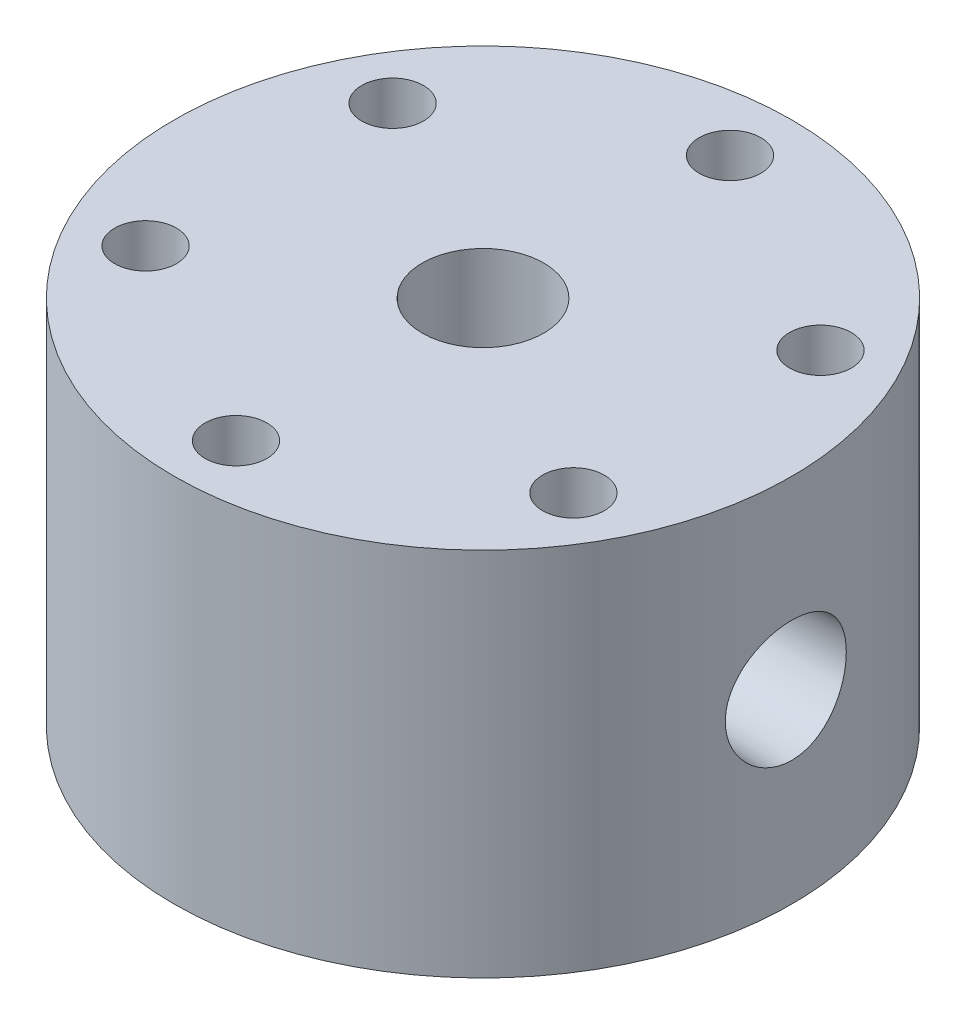
SolidWorks part; units mm, degrees
ref_plane "Front Plane" through (0, 0, 0) normal (0, 0, 1) x (1, 0, 0)
ref_plane "Top Plane" through (0, 0, 0) normal (0, 1, 0) x (1, 0, 0)
ref_plane "Right Plane" through (0, 0, 0) normal (1, 0, 0) x (0, 0, -1)
sketch "Sketch1" plane through (0, 0, 0) normal (0, 0, 1) x (1, 0, 0)
  line L2 (-3.81, 0) -> (-8.0645, 0)
  line L3 (-31.75, -6.35) -> (-31.75, 31.75)
  line L4 (-31.75, 31.75) -> (-3.81, 31.75)
  line L6 (-3.81, 31.75) -> (-3.81, 0)
  line L10 (0, 0) -> (0, 15.7692) construction
  line L11 (-31.75, -6.35) -> (-12.7, -6.35)
  line L12 (-11.1125, 0) -> (-11.1125, 2.032)
  line L13 (-11.1125, 2.032) -> (-8.0645, 2.032)
  line L14 (-8.0645, 2.032) -> (-8.0645, 0)
  line L15 (-11.1125, 0) -> (-12.7, 0)
  line L16 (-12.7, 0) -> (-12.7, -6.35)
  point P1 (0, 0)
  dimension "D1" = 3.81
  dimension "D2" = 1.5875
  dimension "D3" = 12.7
  dimension "D4" = 38.1
  dimension "D5" = 31.75
  dimension "D6" = 6.35
  dimension "D8" = 3.048
  dimension "D9" = 2.032
revolve "Revolve1" add sketch "Sketch1" angle 360 about L10
hole_wizard "M14x1.5 Tapped Hole1" positions "Sketch2" profile "Sketch4" tap size "M14x1.5" standard "ANSI Metric"
sketch "Sketch2" plane through (0, 31.75, 0) normal (0, 1, 0) x (1, 0, 0)
  point P0 (0, 0)
sketch "Sketch4" plane through (0, 31.75, 0) normal (1, 0, 0) x (0, 0, 1)
  line L0 (0, 0) -> (0, 29.1554)
  line L1 (0, 29.1554) -> (6.25, 25.4)
  line L2 (6.25, 25.4) -> (6.25, 0)
  line L5 (6.25, 0) -> (0, 0)
  line L10 (0, 29.1554) -> (-6.25, 25.4) construction
  line L11 (0, -6.35) -> (0, 107.95) construction
  dimension "Tap Drill Dia." = 12.5
  dimension "Tap Drill Depth" = 25.4
  dimension "Drill Angle" = 118
cosmetic thread "Hole Thread3" parameters "D1"=27.94, "D2"=14
ref_plane "Plane1" through (31.75, 0, 0) normal (1, 0, 0) x (0, 0, -1)
ref_plane "Plane2" through (-31.75, 0, 0) normal (-1, 0, 0) x (0, 0, 1)
hole_wizard "1/4 NPT Tapped Hole1" positions "Sketch5" profile "Sketch6" size "1/4" standard "ANSI Inch"
sketch "Sketch5" plane through (31.75, 0, 0) normal (1, 0, 0) x (0, 0, -1)
  line L0 (31.75, 31.75) -> (-31.75, 31.75) construction
  point P0 (0, 12.7)
  dimension "D1" = 19.05
sketch "Sketch6" plane through (31.75, 12.7, 0) normal (0, 1, 0) x (0, 0, -1)
  line L0 (0, 0) -> (0, 20.3603)
  line L1 (5.5626, 17.018) -> (0, 20.3603)
  line L2 (-5.5626, 17.018) -> (0, 20.3603) construction
  line L3 (5.5626, 17.018) -> (5.5626, 9.906)
  line L4 (5.5626, 9.906) -> (5.9437, 9.906)
  line L5 (5.9437, 9.906) -> (6.2403, 0)
  line L6 (-5.9437, 9.906) -> (-6.2403, 0) construction
  line L7 (6.2403, 0) -> (0, 0)
  line L8 (0, -6.35) -> (0, 107.95) construction
  line L11 (-5.5626, 9.906) -> (-5.9437, 9.906) construction
  dimension "Tap Drill Dia." = 11.1252
  dimension "Tap Drill Depth" = 17.018
  dimension "Thread Dia." = 12.4806
  dimension "Thread Angle" = 3.43
  dimension "Thread Depth" = 9.906
  dimension "Drill Angle" = 118
cosmetic thread "Hole Thread1" parameters "D1"=9.906, "D2"=13.7086
hole_wizard "1/4 NPT Tapped Hole2" positions "Sketch7" profile "Sketch8" size "1/4" standard "ANSI Inch"
sketch "Sketch7" plane through (-31.75, 0, 0) normal (-1, 0, 0) x (0, 0, 1)
  line L0 (31.75, 31.75) -> (-31.75, 31.75) construction
  point P0 (0, 12.7)
  dimension "D1" = 19.05
sketch "Sketch8" plane through (-31.75, 12.7, 0) normal (0, 1, 0) x (0, 0, 1)
  line L0 (0, 0) -> (0, 20.3603)
  line L1 (5.5626, 17.018) -> (0, 20.3603)
  line L2 (-5.5626, 17.018) -> (0, 20.3603) construction
  line L3 (5.5626, 17.018) -> (5.5626, 9.906)
  line L4 (5.5626, 9.906) -> (5.9437, 9.906)
  line L5 (5.9437, 9.906) -> (6.2403, 0)
  line L6 (-5.9437, 9.906) -> (-6.2403, 0) construction
  line L7 (6.2403, 0) -> (0, 0)
  line L8 (0, -6.35) -> (0, 107.95) construction
  line L11 (-5.5626, 9.906) -> (-5.9437, 9.906) construction
  dimension "Tap Drill Dia." = 11.1252
  dimension "Tap Drill Depth" = 17.018
  dimension "Thread Dia." = 12.4806
  dimension "Thread Angle" = 3.43
  dimension "Thread Depth" = 9.906
  dimension "Drill Angle" = 118
cosmetic thread "Hole Thread2" parameters "D1"=9.906, "D2"=13.7086
hole_wizard "1/16 (0.0625) Diameter Hole1" positions "Sketch9" profile "Sketch10" hole size "1/16" standard "ANSI Inch"
sketch "Sketch9" plane through (31.75, 0, 0) normal (1, 0, 0) x (0, 0, -1)
  point P0 (0, 12.7)
sketch "Sketch10" plane through (31.75, 12.7, 0) normal (0, 1, 0) x (0, 0, -1)
  line L0 (0, 0) -> (0, 29.0519)
  line L1 (0, 29.0519) -> (0.7937, 28.575)
  line L2 (0.7937, 28.575) -> (0.7937, 0)
  line L5 (0.7937, 0) -> (0, 0)
  line L10 (0, 29.0519) -> (-0.7938, 28.575) construction
  line L11 (0, -6.35) -> (0, 107.95) construction
  dimension "Hole Dia." = 1.5875
  dimension "Hole Depth" = 28.575
  dimension "Drill Angle" = 118
hole_wizard "3/32 (0.09375) Diameter Hole1" positions "Sketch11" profile "Sketch12" hole size "3/32" standard "ANSI Inch"
sketch "Sketch11" plane through (-31.75, 0, 0) normal (-1, 0, 0) x (0, 0, 1)
  point P0 (0, 12.7)
sketch "Sketch12" plane through (-31.75, 12.7, 0) normal (0, 1, 0) x (0, 0, 1)
  line L0 (0, 0) -> (0, 29.4174)
  line L1 (0, 29.4174) -> (1.1906, 28.702)
  line L2 (1.1906, 28.702) -> (1.1906, 0)
  line L5 (1.1906, 0) -> (0, 0)
  line L10 (0, 29.4174) -> (-1.1906, 28.702) construction
  line L11 (0, -6.35) -> (0, 107.95) construction
  dimension "Hole Dia." = 2.3812
  dimension "Hole Depth" = 28.702
  dimension "Drill Angle" = 118
hole_wizard "1/4 (0.25) Diameter Hole1" positions "Sketch15" profile "Sketch16" hole size "1/4" standard "ANSI Inch" end condition through all
sketch "Sketch15" plane through (0, 31.75, 0) normal (0, 1, 0) x (1, 0, 0)
  line L0 (0, 0) -> (16.0984, 0) construction
  line L2 (0, 0) -> (21.997, 12.7) construction
  point P0 (21.997, 12.7)
  dimension "D1" = 25.4
  dimension "D2" = 30
sketch "Sketch16" plane through (21.997, 31.75, -12.7) normal (1, 0, 0) x (0, 0, 1)
  line L0 (0, 0) -> (0, 38.1)
  line L1 (0, 38.1) -> (3.175, 38.1)
  line L2 (3.175, 38.1) -> (3.175, 0)
  line L5 (3.175, 0) -> (0, 0)
  line L11 (0, -6.35) -> (0, 107.95) construction
  dimension "Thru Hole Dia." = 6.35
  dimension "Thru Hole Depth" = 38.1
pattern_circular "CirPattern1" count 6 over 360 about axis through (0, 0, 0) along (0, 1, 0) of "1/4 (0.25) Diameter Hole1"
ref_plane "Plane3" through (15.875, 0, -27.4963) normal (0.5, 0, -0.866) x (0, -1, 0)
hole_wizard "1/4 NPT Tapped Hole3" positions "Sketch17" profile "Sketch18" size "1/4" standard "ANSI Inch"
sketch "Sketch17" plane through (15.875, 0, -27.4963) normal (0.5, 0, -0.866) x (0, -1, 0)
  point P0 (-12.7, 0)
  point P4 (-12.4632, 0)
  dimension "D1" = 12.7
sketch "Sketch18" plane through (15.875, 12.7, -27.4963) normal (0, 1, 0) x (-0.866, 0, -0.5)
  line L0 (0, 0) -> (0, 19.8523)
  line L1 (5.5626, 16.51) -> (0, 19.8523)
  line L2 (-5.5626, 16.51) -> (0, 19.8523) construction
  line L3 (5.5626, 16.51) -> (5.5626, 12.7)
  line L4 (5.5626, 12.7) -> (6.558, 12.7)
  line L5 (6.558, 12.7) -> (6.9382, 0)
  line L6 (-6.558, 12.7) -> (-6.9382, 0) construction
  line L7 (6.9382, 0) -> (0, 0)
  line L8 (0, -6.35) -> (0, 107.95) construction
  line L11 (-5.5626, 12.7) -> (-6.558, 12.7) construction
  dimension "Tap Drill Dia." = 11.1252
  dimension "Tap Drill Depth" = 16.51
  dimension "Thread Dia." = 13.8765
  dimension "Thread Angle" = 3.43
  dimension "Thread Depth" = 12.7
  dimension "Drill Angle" = 118
hole_wizard "1/32 (0.03125) Diameter Hole1" positions "Sketch19" profile "Sketch20" hole size "1/32" standard "ANSI Inch"
sketch "Sketch19" plane through (15.875, 0, -27.4963) normal (0.5, 0, -0.866) x (0, -1, 0)
  point P0 (-12.7, 0)
sketch "Sketch20" plane through (15.875, 12.7, -27.4963) normal (0, 1, 0) x (-0.866, 0, -0.5)
  line L0 (0, 0) -> (0, 28.8135)
  line L1 (0, 28.8135) -> (0.3969, 28.575)
  line L2 (0.3969, 28.575) -> (0.3969, 0)
  line L5 (0.3969, 0) -> (0, 0)
  line L10 (0, 28.8135) -> (-0.3969, 28.575) construction
  line L11 (0, -6.35) -> (0, 107.95) construction
  dimension "Hole Dia." = 0.7937
  dimension "Hole Depth" = 28.575
  dimension "Drill Angle" = 118
